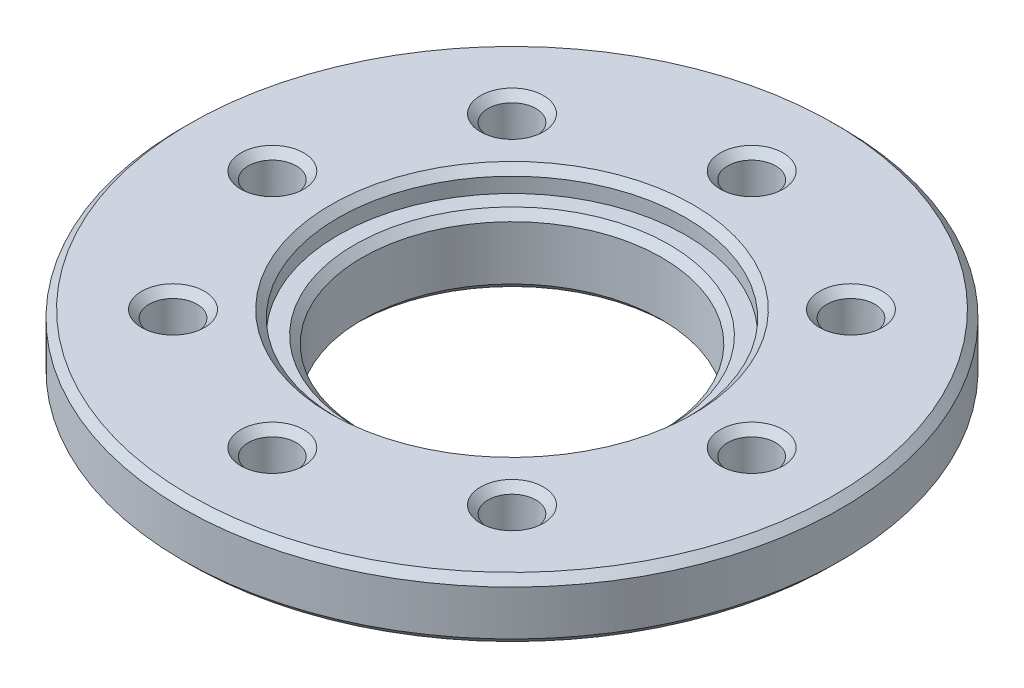
SolidWorks part; units mm, degrees
ref_plane "Front Plane" through (0, 0, 0) normal (0, 0, 1) x (1, 0, 0)
ref_plane "Top Plane" through (0, 0, 0) normal (0, 1, 0) x (1, 0, 0)
ref_plane "Right Plane" through (0, 0, 0) normal (1, 0, 0) x (0, 0, -1)
sketch "Sketch1" plane through (0, 0, 0) normal (0, 0, 1) x (1, 0, 0)
  line L0 (11, 0) -> (0, 0)
  line L1 (0, 0) -> (0, -2)
  line L2 (0, -2) -> (11, -2)
  line L3 (11, -2) -> (11, 0)
  line L4 (0, 0) -> (0, -2) construction
revolve "Revolve1" add sketch "Sketch1" angle 360 about L4
sketch "Sketch2" plane through (0, -2, 0) normal (0, -1, 0) x (1, 0, 0)
  circle A0 centre (0, 0) radius 6.25
extrude "Boss-Extrude1" add sketch "Sketch2" along normal blind 1.05
hole_wizard "Hole1" positions "Sketch4" profile "Sketch3" legacy
sketch "Sketch4" plane through (0, 0, 0) normal (0, 1, 0) x (1, 0, 0)
  point P0 (0, 8)
  point P1 (5.6569, 5.6569)
  point P2 (8, 0)
  point P3 (5.6569, -5.6569)
  point P4 (0, -8)
  point P5 (-5.6569, -5.6569)
  point P6 (-8, 0)
  point P7 (-5.6569, 5.6569)
sketch "Sketch3" plane through (0, 0, -8) normal (1, 0, 0) x (0, 0, 1)
  line L0 (0, 0) -> (0, 3.05)
  line L1 (0, 3.05) -> (0.8, 3.05)
  line L2 (0.8, 3.05) -> (0.8, 0)
  line L3 (0.8, 0) -> (0, 0)
  line L4 (0, 110) -> (0, -10) construction
  dimension "Diameter" = 1.6
  dimension "Depth" = 3.05
hole_wizard "CBORE for 3/8 Binding Head Machine Screw1" positions "Sketch6" profile "Sketch5" counterbore size "3/8" standard "ANSI Inch"
sketch "Sketch6" plane through (0, 0, 0) normal (0, 1, 0) x (1, 0, 0)
  point P0 (0, 0)
sketch "Sketch5" plane through (0, 0, 0) normal (1, 0, 0) x (0, 0, 1)
  line L0 (0, 0) -> (0, 3.05)
  line L1 (0, 3.05) -> (5, 3.05)
  line L3 (5, 3.05) -> (5, 0.75)
  line L4 (5, 0.75) -> (5.8, 0.75)
  line L5 (5.8, 0.75) -> (5.8, 0)
  line L7 (5.8, 0) -> (0, 0)
  line L11 (0, -6.35) -> (0, 107.95) construction
  dimension "Thru Hole Dia." = 10
  dimension "Thru Hole Depth" = 3.05
  dimension "C'Bore Dia." = 11.6
  dimension "C'Bore Depth" = 0.75
chamfer "Chamfer1" distance 0.25 angle 45 14 edges at (8, 0, 0.8) (-8, 0, 0.8) (0, 0, 8.8) (0, -3.05, 5) (0, -2, -11) (0, 0, 5.8) (5.6569, 0, 6.4569) (0, 0, -11) (-5.6569, 0, 6.4569) (0, -3.05, -6.25) (-5.6569, 0, -4.8569) (0, 0, -7.2) (0, -0.75, 5) (5.6569, 0, -4.8569)
